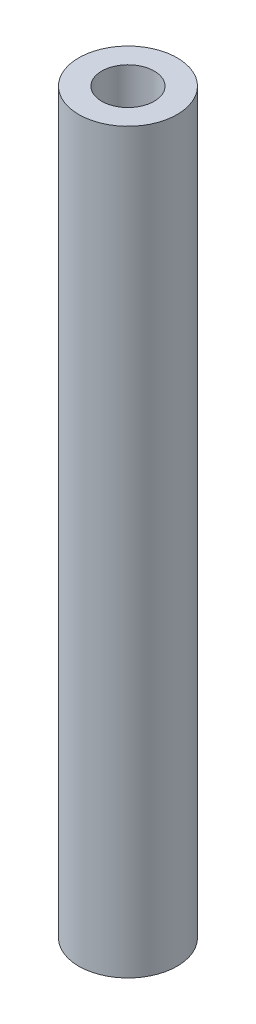
SolidWorks part; units mm, degrees
ref_plane "前视基准面" through (0, 0, 0) normal (0, 0, 1) x (1, 0, 0)
ref_plane "上视基准面" through (0, 0, 0) normal (0, 1, 0) x (1, 0, 0)
ref_plane "右视基准面" through (0, 0, 0) normal (1, 0, 0) x (0, 0, -1)
sketch "草图1" plane through (0, 0, 0) normal (0, 1, 0) x (1, 0, 0)
  circle A0 centre (0, 0) radius 3
  circle A1 centre (0, 0) radius 1.6
  dimension "D1" = 3.2
  dimension "D2" = 6
extrude "凸台-拉伸1" add sketch "草图1" along normal blind 45
